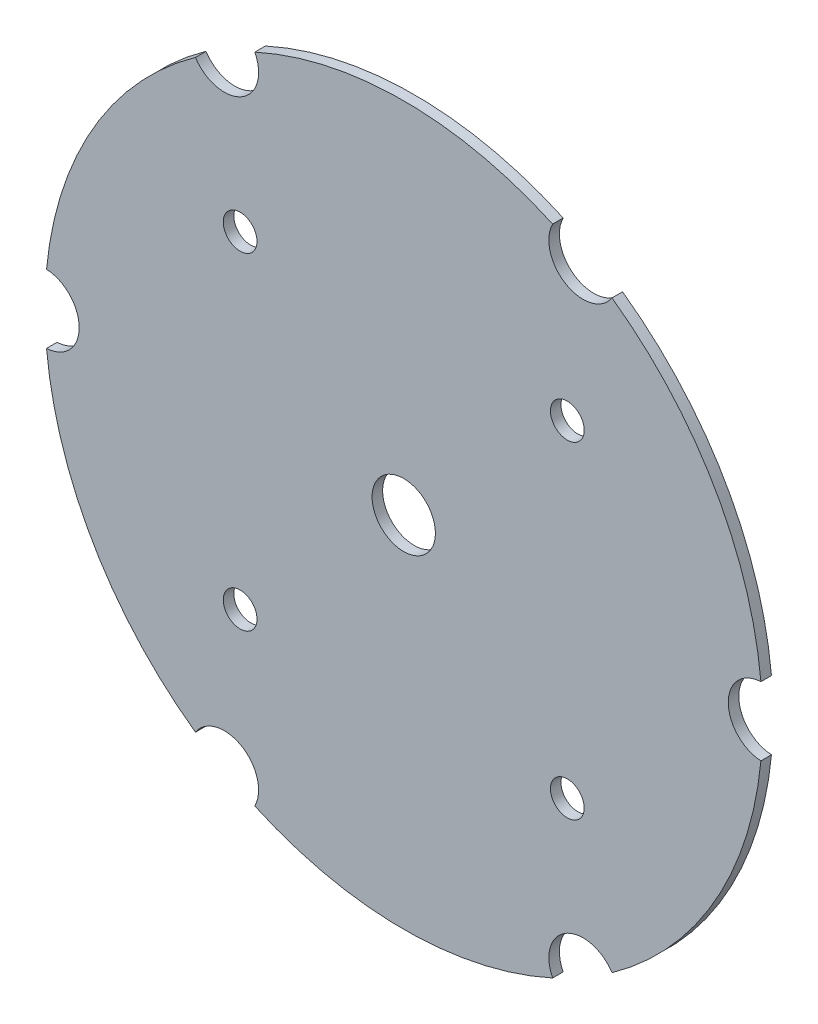
SolidWorks part; units mm, degrees
ref_plane "Plan de face" through (0, 0, 0) normal (0, 0, 1) x (1, 0, 0)
ref_plane "Plan de dessus" through (0, 0, 0) normal (0, 1, 0) x (1, 0, 0)
ref_plane "Plan de droite" through (0, 0, 0) normal (1, 0, 0) x (0, 0, -1)
sketch "Esquisse1" plane through (0, 0, 0) normal (0, 0, 1) x (1, 0, 0)
  line L0 (0, 0) -> (0, -34) construction
  line L1 (0, 0) -> (-17, -29.4449) construction
  line L3 (-15.5, -15.5) -> (15.5, -15.5) construction
  line L4 (-15.5, -15.5) -> (-15.5, 15.5) construction
  line L5 (-15.5, 15.5) -> (15.5, 15.5) construction
  line L6 (15.5, -15.5) -> (15.5, 15.5) construction
  line L7 (-15.5, -15.5) -> (15.5, 15.5) construction
  line L8 (-15.5, 15.5) -> (15.5, -15.5) construction
  circle A0 centre (0, 0) radius 34
  circle A1 centre (-17, -29.4449) radius 3.25
  circle A2 centre (-34, 0) radius 3.25
  circle A3 centre (-17, 29.4449) radius 3.25
  circle A4 centre (17, 29.4449) radius 3.25
  circle A5 centre (34, 0) radius 3.25
  circle A6 centre (17, -29.4449) radius 3.25
  circle A7 centre (0, 0) radius 3
  circle A8 centre (-15.5, 15.5) radius 1.6
  circle A9 centre (15.5, 15.5) radius 1.6
  circle A10 centre (15.5, -15.5) radius 1.6
  circle A11 centre (-15.5, -15.5) radius 1.6
  point P19 (0, 0)
  dimension "D1" = 68
  dimension "D2" = 6.5
  dimension "D5" = 6
  dimension "D8" = 3.2
  dimension "D3" = 30
  dimension "D6" = 31
  dimension "D7" = 31
  dimension "D4" = 6
extrude "Boss.-Extru.1" add sketch "Esquisse1" along normal blind 1 contours A6 A0 A5 A4 A3 A2 A1 A11 A10 A9 A8 A7
